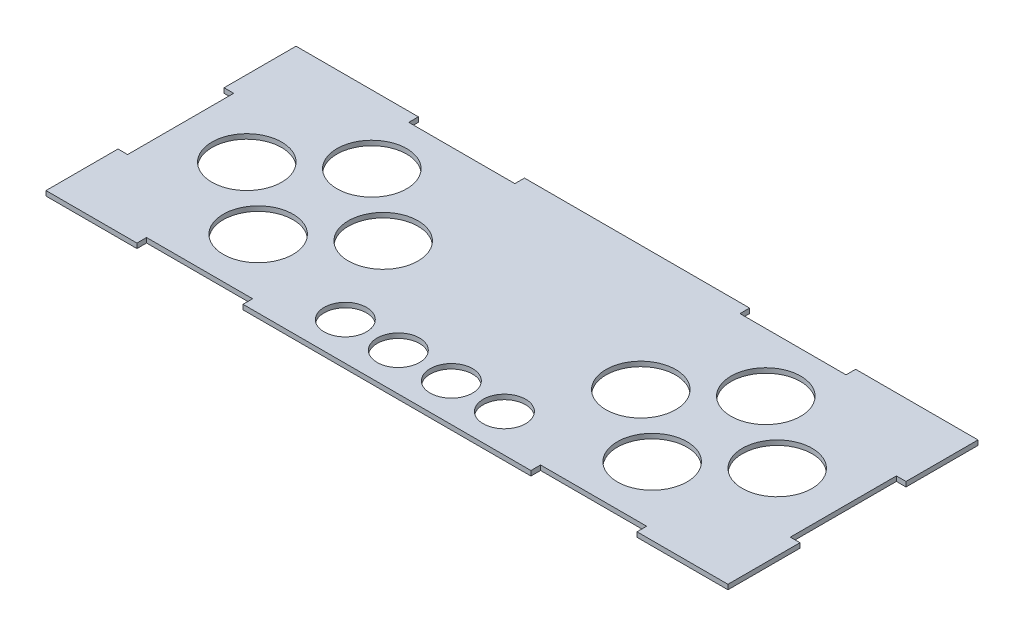
SolidWorks part; units mm, degrees
ref_plane "Front Plane" through (0, 0, 0) normal (0, 0, 1) x (1, 0, 0)
ref_plane "Top Plane" through (0, 0, 0) normal (0, 1, 0) x (1, 0, 0)
ref_plane "Right Plane" through (0, 0, 0) normal (1, 0, 0) x (0, 0, -1)
sketch "Sketch1" plane through (0, 0, 0) normal (0, 1, 0) x (1, 0, 0)
  line L0 (74.275, 82.5) -> (-74.275, 82.5)
  line L1 (225, -82.5) -> (165, -82.5)
  line L2 (225, -82.5) -> (225, -35)
  line L3 (225, 82.5) -> (144.275, 82.5)
  line L4 (-225, -82.5) -> (-225, -35)
  line L5 (225, -82.5) -> (-225, 82.5) construction
  line L6 (225, 82.5) -> (-225, -82.5) construction
  line L8 (-165, -82.5) -> (-165, -76.15)
  line L9 (-165, -76.15) -> (-95, -76.15)
  line L10 (-95, -82.5) -> (-95, -76.15)
  line L12 (95, -82.5) -> (95, -76.15)
  line L13 (95, -76.15) -> (165, -76.15)
  line L14 (165, -82.5) -> (165, -76.15)
  line L15 (-225, -35) -> (-218.65, -35)
  line L17 (-225, 35) -> (-218.65, 35)
  line L18 (-218.65, -35) -> (-218.65, 35)
  line L19 (225, -35) -> (218.65, -35)
  line L21 (225, 35) -> (218.65, 35)
  line L22 (218.65, -35) -> (218.65, 35)
  line L24 (-144.275, 82.5) -> (-144.275, 76.15)
  line L25 (-144.275, 76.15) -> (-74.275, 76.15)
  line L26 (-74.275, 82.5) -> (-74.275, 76.15)
  line L28 (74.275, 82.5) -> (74.275, 76.15)
  line L29 (74.275, 76.15) -> (144.275, 76.15)
  line L30 (144.275, 82.5) -> (144.275, 76.15)
  line L31 (225, 35) -> (225, 82.5)
  line L32 (95, -82.5) -> (-95, -82.5)
  line L33 (-165, -82.5) -> (-225, -82.5)
  line L34 (-225, 35) -> (-225, 82.5)
  line L35 (-144.275, 82.5) -> (-225, 82.5)
  circle A0 centre (-130, 37.5) radius 23
  circle A1 centre (-85, 0) radius 23
  circle A2 centre (-175, 0) radius 23
  circle A3 centre (-130, -37.5) radius 23
  circle A4 centre (130, 37.5) radius 23
  circle A5 centre (85, 0) radius 23
  circle A6 centre (175, 0) radius 23
  circle A7 centre (130, -37.5) radius 23
  circle A8 centre (-52.5, -57.5) radius 14
  circle A9 centre (-17.5, -57.5) radius 14
  circle A10 centre (17.5, -57.5) radius 14
  circle A11 centre (52.5, -57.5) radius 14
  point P0 (0, 0)
  point P39 (-130, -76.15)
  dimension "D3" = 46
  dimension "D4" = 46
  dimension "D5" = 46
  dimension "D6" = 46
  dimension "D7" = 50
  dimension "D8" = 82.5
  dimension "D9" = 45
  dimension "D10" = 95
  dimension "D11" = 95
  dimension "D12" = 45
  dimension "D13" = 82.5
  dimension "D14" = 140
  dimension "D15" = 45
  dimension "D16" = 45
  dimension "D17" = 50
  dimension "D18" = 140
  dimension "D19" = 95
  dimension "D20" = 95
  dimension "D21" = 46
  dimension "D22" = 46
  dimension "D23" = 46
  dimension "D24" = 46
  dimension "D25" = 82.5
  dimension "D26" = 82.5
  dimension "D27" = 28
  dimension "D28" = 28
  dimension "D29" = 28
  dimension "D30" = 28
  dimension "D31" = 25
  dimension "D32" = 35
  dimension "D33" = 35
  dimension "D34" = 35
  dimension "D35" = 25
  dimension "D36" = 25
  dimension "D37" = 25
  dimension "D38" = 172.5
  dimension "D1" = 450
  dimension "D2" = 165
  dimension "D39" = 70
  dimension "D40" = 70
  dimension "D41" = 6.35
  dimension "D42" = 6.35
  dimension "D43" = 60
  dimension "D44" = 70
  dimension "D45" = 6.35
  dimension "D46" = 47.5
  dimension "D47" = 70
  dimension "D48" = 6.35
  dimension "D49" = 47.5
  dimension "D50" = 60
  dimension "D51" = 6.35
  dimension "D52" = 70
  dimension "D53" = 80.725
  dimension "D54" = 70
  dimension "D55" = 6.35
  dimension "D56" = 80.725
extrude "Boss-Extrude1" add sketch "Sketch1" along normal blind 3.175
